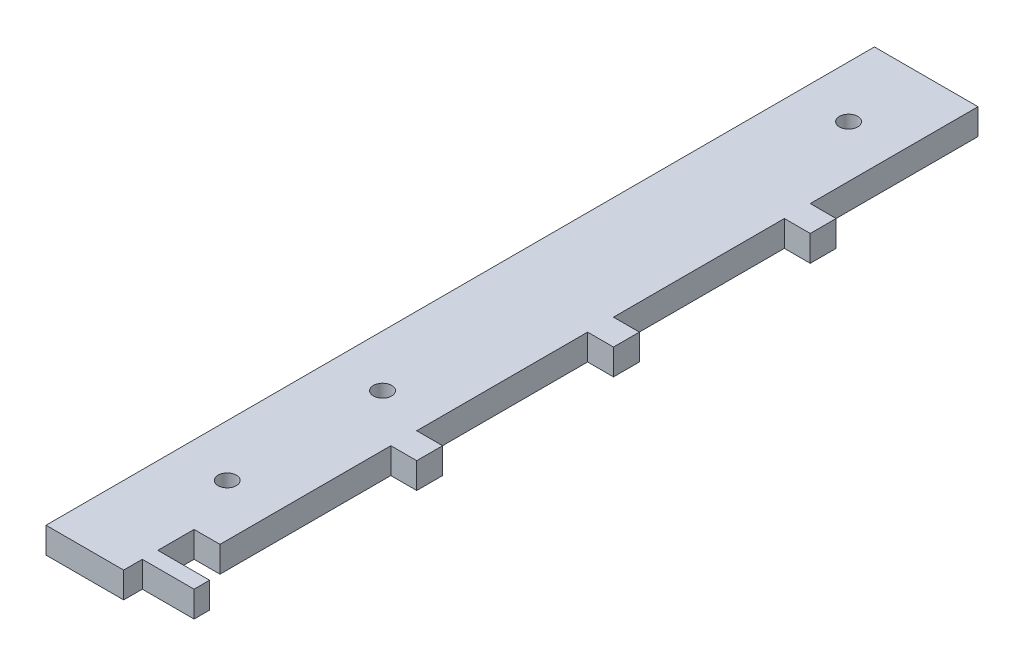
SolidWorks part; units mm, degrees
ref_plane "Front Plane" through (0, 0, 0) normal (0, 0, 1) x (1, 0, 0)
ref_plane "Top Plane" through (0, 0, 0) normal (0, 1, 0) x (1, 0, 0)
ref_plane "Right Plane" through (0, 0, 0) normal (1, 0, 0) x (0, 0, -1)
sketch "Sketch1" plane through (0, 0, 0) normal (0, 1, 0) x (1, 0, 0)
  line L0 (0, 0) -> (31.75, 0)
  line L1 (0, 0) -> (0, 203.2)
  line L2 (31.75, 0) -> (31.75, 203.2)
  line L3 (0, 203.2) -> (31.75, 203.2)
  dimension "D1" = 31.75
  dimension "D2" = 203.2
extrude "Boss-Extrude1" add sketch "Sketch1" along normal blind 6.35
sketch "Sketch2" plane through (0, 6.35, 0) normal (0, 1, 0) x (1, 0, 0)
  line L0 (31.75, 0) -> (31.75, 203.2) construction
  line L1 (31.75, 203.2) -> (25.4, 203.2)
  line L2 (31.75, 203.2) -> (31.75, 162.052)
  line L3 (31.75, 162.052) -> (25.4, 162.052)
  line L4 (25.4, 203.2) -> (25.4, 162.052)
  line L5 (31.75, 155.702) -> (25.4, 155.702)
  line L6 (31.75, 155.702) -> (31.75, 113.792)
  line L7 (31.75, 113.792) -> (25.4, 113.792)
  line L8 (25.4, 155.702) -> (25.4, 113.792)
  line L9 (31.75, 107.442) -> (31.75, 17.272)
  line L10 (31.75, 107.442) -> (25.4, 107.442)
  line L12 (31.75, 65.532) -> (25.4, 65.532)
  line L13 (25.4, 107.442) -> (25.4, 65.532)
  line L18 (31.75, 0) -> (19.05, 0)
  line L19 (31.75, 0) -> (31.75, 4.572)
  line L20 (31.75, 4.572) -> (19.05, 4.572)
  line L21 (19.05, 0) -> (19.05, 4.572)
  line L22 (31.75, 8.382) -> (19.05, 8.382)
  line L23 (31.75, 8.382) -> (31.75, 17.272)
  line L24 (31.75, 17.272) -> (19.05, 17.272)
  line L25 (19.05, 8.382) -> (19.05, 17.272)
  line L26 (31.75, 59.182) -> (25.4, 59.182)
  line L29 (25.4, 59.182) -> (25.4, 17.272)
  dimension "D1" = 4.572
  dimension "D2" = 3.81
  dimension "D3" = 8.89
  dimension "D4" = 12.7
  dimension "D5" = 12.7
  dimension "D6" = 41.91
  dimension "D7" = 6.35
  dimension "D8" = 6.35
  dimension "D9" = 6.35
  dimension "D10" = 6.35
  dimension "D11" = 41.91
  dimension "D12" = 6.35
  dimension "D13" = 41.91
  dimension "D14" = 6.35
extrude "Cut-Extrude1" cut sketch "Sketch2" against normal through all
hole_wizard "CBORE for #8 Binding Head Machine Screw1" positions "Sketch3" profile "Sketch4" counterbore size "#8" standard "ANSI Inch" end condition through all
sketch "Sketch3" plane through (0, 0, 0) normal (0, -1, 0) x (-1, 0, 0)
  line L0 (0, 203.2) -> (0, 0) construction
  line L1 (0, 0) -> (-19.05, 0) construction
  line L2 (-25.4, 203.2) -> (0, 203.2) construction
  point P0 (-12.7, 31.75)
  point P7 (-12.7, 69.85)
  point P10 (-12.7, 184.15)
  dimension "D1" = 12.7
  dimension "D2" = 31.75
  dimension "D3" = 38.1
  dimension "D4" = 19.05
sketch "Sketch4" plane through (12.7, 0, -31.75) normal (1, 0, 0) x (0, 0, -1)
  line L0 (0, 0) -> (0, 6.35)
  line L1 (0, 6.35) -> (2.2479, 6.35)
  line L3 (2.2479, 6.35) -> (2.2479, 3.175)
  line L4 (2.2479, 3.175) -> (4.7625, 3.175)
  line L5 (4.7625, 3.175) -> (4.7625, 0)
  line L7 (4.7625, 0) -> (0, 0)
  line L11 (0, -6.35) -> (0, 107.95) construction
  dimension "Thru Hole Dia." = 4.4958
  dimension "Thru Hole Depth" = 6.35
  dimension "C'Bore Dia." = 9.525
  dimension "C'Bore Depth" = 3.175
